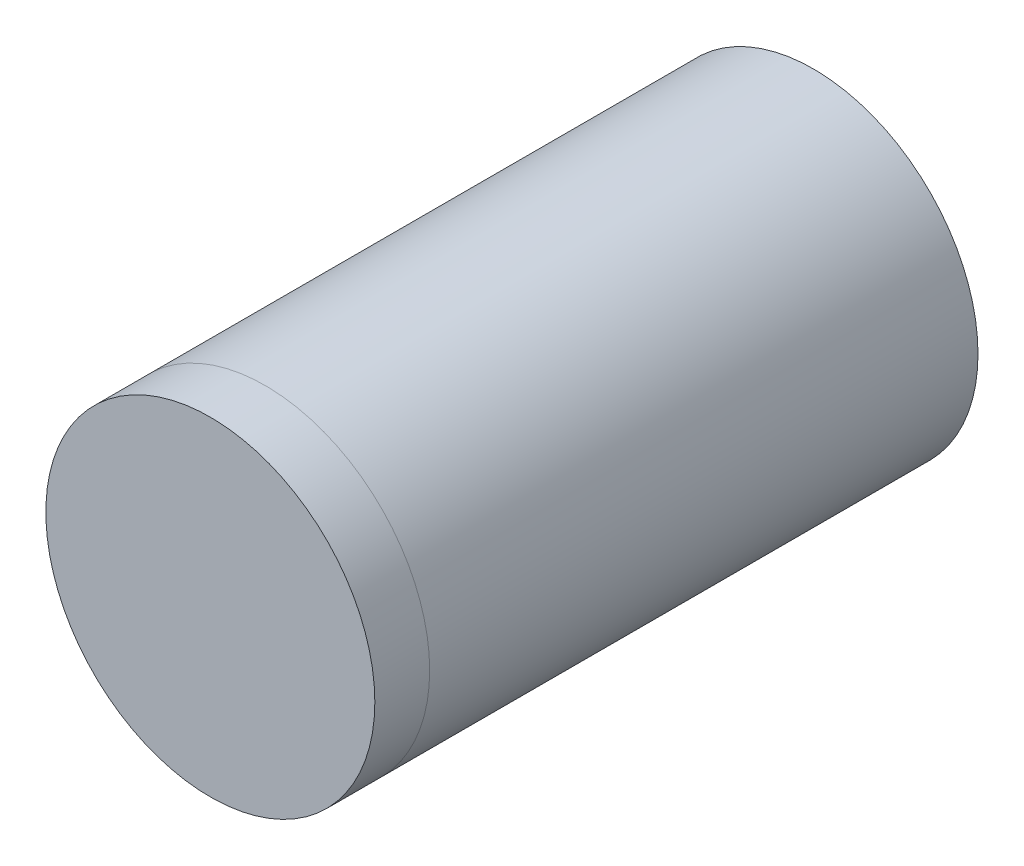
SolidWorks part; units mm, degrees
ref_plane "Front Plane" through (0, 0, 0) normal (0, 0, 1) x (1, 0, 0)
ref_plane "Top Plane" through (0, 0, 0) normal (0, 1, 0) x (1, 0, 0)
ref_plane "Right Plane" through (0, 0, 0) normal (1, 0, 0) x (0, 0, -1)
sketch "Sketch1" plane through (0, 0, 0) normal (0, 0, 1) x (1, 0, 0)
  circle A0 centre (0, 0) radius 9
  dimension "D1" = 18
extrude "Boss-Extrude1" add sketch "Sketch1" along normal blind 30
sketch "Sketch2" plane through (0, 0, 30) normal (0, 0, 1) x (1, 0, 0)
  circle A0 centre (0, 0) radius 9
extrude "Boss-Extrude2" add sketch "Sketch2" along normal blind 3 separate body
